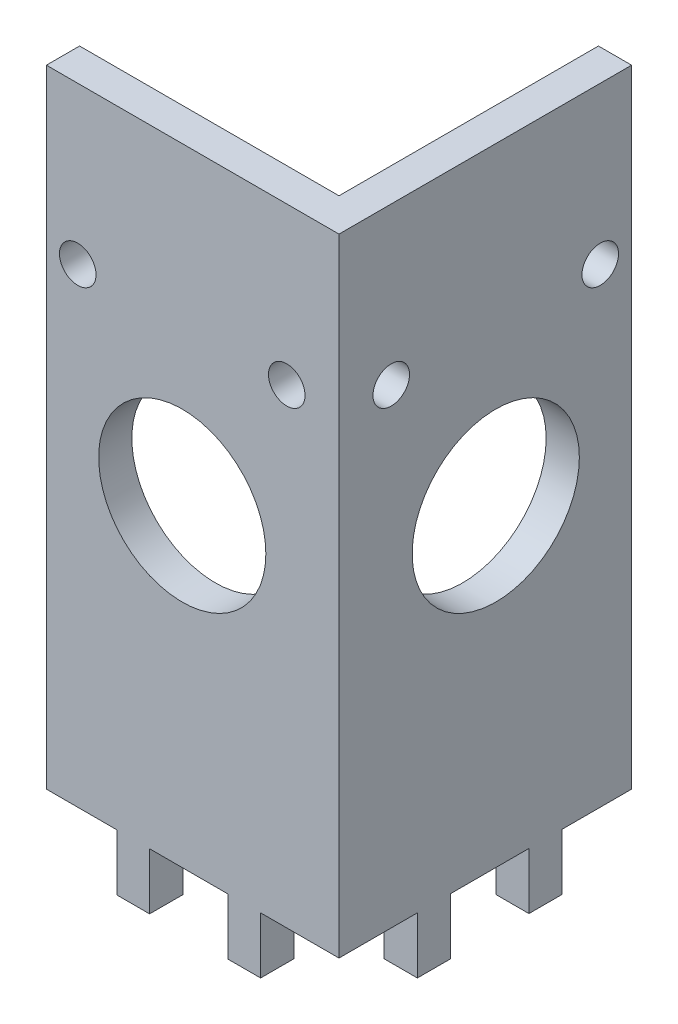
SolidWorks part; units mm, degrees
ref_plane "Front Plane" through (0, 0, 0) normal (0, 0, 1) x (1, 0, 0)
ref_plane "Top Plane" through (0, 0, 0) normal (0, 1, 0) x (1, 0, 0)
ref_plane "Right Plane" through (0, 0, 0) normal (1, 0, 0) x (0, 0, -1)
sketch "Sketch1" plane through (0, 0, 0) normal (0, 1, 0) x (1, 0, 0)
  line L0 (0, 0) -> (-50.5, 0) construction
  line L1 (0, 0) -> (0, 50.5) construction
  line L2 (-50.5, 22.5) -> (-22.5, 22.5)
  line L3 (-22.5, 22.5) -> (-22.5, 50.5)
  line L5 (-22.5, 22.5) -> (-50.5, 22.5)
  line L6 (-22.5, 22.5) -> (-22.5, 25.675)
  line L7 (-22.5, 25.675) -> (-50.5, 25.675)
  line L8 (-50.5, 22.5) -> (-50.5, 25.675)
  line L9 (-22.5, 22.5) -> (-25.675, 22.5)
  line L10 (-22.5, 22.5) -> (-22.5, 50.5)
  line L11 (-22.5, 50.5) -> (-25.675, 50.5)
  line L12 (-25.675, 22.5) -> (-25.675, 50.5)
  point P7 (-37.5, 22.5)
  point P8 (-22.5, 37.5)
  dimension "D1" = 50.5
  dimension "D2" = 50.5
  dimension "D3" = 22.5
  dimension "D4" = 22.5
  dimension "D5" = 37.5
  dimension "D6" = 37.5
  dimension "D7" = 28
  dimension "D8" = 28
  dimension "D9" = 3.175
  dimension "D10" = 3.175
extrude "Boss-Extrude1" add sketch "Sketch1" along normal blind 60 contours L2 L12 L7 L8 | L12 L5 L3 L7 | L12 L7 L3 L11
sketch "Sketch2" plane through (0, 0, -22.5) normal (0, 0, 1) x (1, 0, 0)
  line L0 (-50.5, 30) -> (-22.5, 30) construction
  line L1 (-50.5, 60) -> (-50.5, 0) construction
  line L2 (-22.5, 60) -> (-22.5, 0) construction
  line L3 (-37.5, 60) -> (-37.5, 0) construction
  line L4 (-50.5, 60) -> (-22.5, 60) construction
  line L5 (-50.5, 0) -> (-22.5, 0) construction
  line L7 (-50.5, 60) -> (-22.5758, 60)
  line L15 (-33.125, -5.4) -> (-33.125, 0)
  line L16 (-30, -5.4) -> (-33.125, -5.4)
  line L17 (-30, -5.4) -> (-30, 0)
  line L18 (-40.625, -5.4) -> (-40.625, 0)
  line L19 (-43.75, -5.4) -> (-40.625, -5.4)
  line L20 (-43.75, -5.4) -> (-43.75, 0)
  circle A0 centre (-37.5, 30) radius 8
  dimension "D2" = 16
  dimension "D1" = 15
  dimension "D3" = 5.4
  dimension "D4" = 7.5
  dimension "D6" = 3.125
  dimension "D5" = 7.5
sketch "Sketch3" plane through (-22.5, 0, 0) normal (1, 0, 0) x (0, 0, -1)
  line L0 (22.5, 30) -> (50.5, 30) construction
  line L1 (22.5, 60) -> (22.5, 0) construction
  line L2 (50.5, 60) -> (50.5, 0) construction
  line L3 (37.5, 60) -> (37.5, 0) construction
  line L4 (22.5, 60) -> (50.5, 60) construction
  line L5 (22.5, 0) -> (50.5, 0) construction
  circle A0 centre (37.5, 30) radius 8
  dimension "D1" = 16
  dimension "D2" = 15
extrude "Boss-Extrude4" add sketch "Sketch2" against normal blind 3.175
sketch "Sketch4" plane through (0, 0, -22.5) normal (0, 0, 1) x (1, 0, 0)
  line L0 (-50.5, 30) -> (-22.5, 30) construction
  line L1 (-50.5, 60) -> (-50.5, 0) construction
  line L2 (-22.5, 22) -> (-22.5, 38) construction
  line L3 (-37.5, 60) -> (-37.5, 0) construction
  line L4 (-50.5, 60) -> (-22.5, 60) construction
  line L5 (-50.5, 0) -> (-43.75, 0) construction
  line L6 (-22.5, 60) -> (-22.5, 0) construction
  circle A0 centre (-37.5, 30) radius 8
  dimension "D1" = 16
  dimension "D2" = 15
extrude "Cut-Extrude1" cut sketch "Sketch4" against normal blind 3.175
extrude "Cut-Extrude2" cut sketch "Sketch3" against normal blind 3.175
sketch "Sketch5" plane through (-22.5, 0, 0) normal (1, 0, 0) x (0, 0, -1)
  line L0 (22.5, 0) -> (50.5, 0) construction
  line L1 (22.5, 60) -> (50.5, 60)
  line L10 (22.5, 30) -> (50.5, 30) construction
  line L11 (22.5, 60) -> (22.5, 0) construction
  line L12 (50.5, 60) -> (50.5, 0) construction
  line L13 (43.85, -5.4) -> (43.85, 0)
  line L14 (40.675, -5.4) -> (43.85, -5.4)
  line L15 (40.675, -5.4) -> (40.675, 0)
  line L16 (33.175, -5.4) -> (33.175, 0)
  line L17 (30, -5.4) -> (33.175, -5.4)
  line L18 (30, -5.4) -> (30, 0)
  line L19 (30, 0) -> (33.175, 0)
  line L28 (40.675, 0) -> (43.85, 0)
  point P7 (37.5, 30)
  point P8 (-4.2304, -0.8722)
  point P10 (8.5502, 17.2274)
  dimension "D1" = 7.5
  dimension "D2" = 5.4
  dimension "D3" = 3.175
  dimension "D4" = 7.5
extrude "Boss-Extrude5" add sketch "Sketch5" against normal blind 3.175
sketch "Sketch6" plane through (0, 0, -22.5) normal (0, 0, 1) x (1, 0, 0)
  line L0 (-50.5, 45) -> (-22.5, 45) construction
  line L1 (-50.5, 60) -> (-50.5, 0) construction
  line L2 (-22.5, 60) -> (-22.5, 0) construction
  line L3 (-37.5, 60) -> (-37.5, 0) construction
  line L4 (-50.5, 60) -> (-22.5, 60) construction
  line L5 (-40.625, 0) -> (-33.125, 0) construction
  circle A0 centre (-37.5, 30) radius 8 construction
  circle A1 centre (-37.5, 30) radius 8 construction
  circle A2 centre (-47.5, 45) radius 1.75
  circle A3 centre (-27.5, 45) radius 1.75
  dimension "D1" = 15
  dimension "D3" = 3.5
  dimension "D2" = 10
extrude "Cut-Extrude3" cut sketch "Sketch6" against normal blind 10 contours A2 | A3
sketch "Sketch7" plane through (-22.5, 0, 0) normal (1, 0, 0) x (0, 0, -1)
  line L0 (37.5, 60) -> (37.5, 0) construction
  line L1 (22.5, 60) -> (50.5, 60) construction
  line L2 (33.175, 0) -> (40.675, 0) construction
  line L4 (22.5, 60) -> (22.5, 0) construction
  line L5 (22.5, 45) -> (50.5, 45) construction
  line L6 (50.5, 60) -> (50.5, 0) construction
  circle A0 centre (37.5, 30) radius 8 construction
  circle A1 centre (37.5, 30) radius 8 construction
  circle A2 centre (47.5, 45) radius 1.75
  circle A3 centre (27.5, 45) radius 1.75
  dimension "D1" = 15
  dimension "D3" = 3.5
  dimension "D2" = 10
extrude "Cut-Extrude4" cut sketch "Sketch7" against normal blind 10
equation "\"wall width\"=5.05"
equation "\"D1@Sketch1\"=\"wall width\""
equation "\"D2@Sketch1\"=\"wall width\""
equation "\"belt traveling width\"=2.25"
equation "\"D3@Sketch1\"=\"belt traveling width\""
equation "\"D4@Sketch1\"=\"belt traveling width\""
equation "\"bearing center\"=3.75"
equation "\"D5@Sketch1\"=\"bearing center\""
equation "\"D6@Sketch1\"=\"bearing center\""
equation "\"bearing holder wall width\"=2.8"
equation "\"D7@Sketch1\"=\"bearing holder wall width\""
equation "\"D8@Sketch1\"=\"bearing holder wall width\""
equation "\"wall thickness\"=0.3175"
equation "\"D9@Sketch1\"=\"wall thickness\""
equation "\"D10@Sketch1\"=\"wall thickness\""
equation "\"off wall bearing distance\"=1.5"
equation "\"D1@Sketch2\"=\"off wall bearing distance\""
equation "\"bearing diameter\"=1.6"
equation "\"D2@Sketch2\"=\"bearing diameter\""
equation "\"D1@Sketch3\"=\"bearing diameter\""
equation "\"D2@Sketch3\"=\"off wall bearing distance\""
equation "\"tooth width\"=0.75"
equation "\"D1@Sketch4\"=\"bearing diameter\""
equation "\"D2@Sketch4\"=\"off wall bearing distance\""
